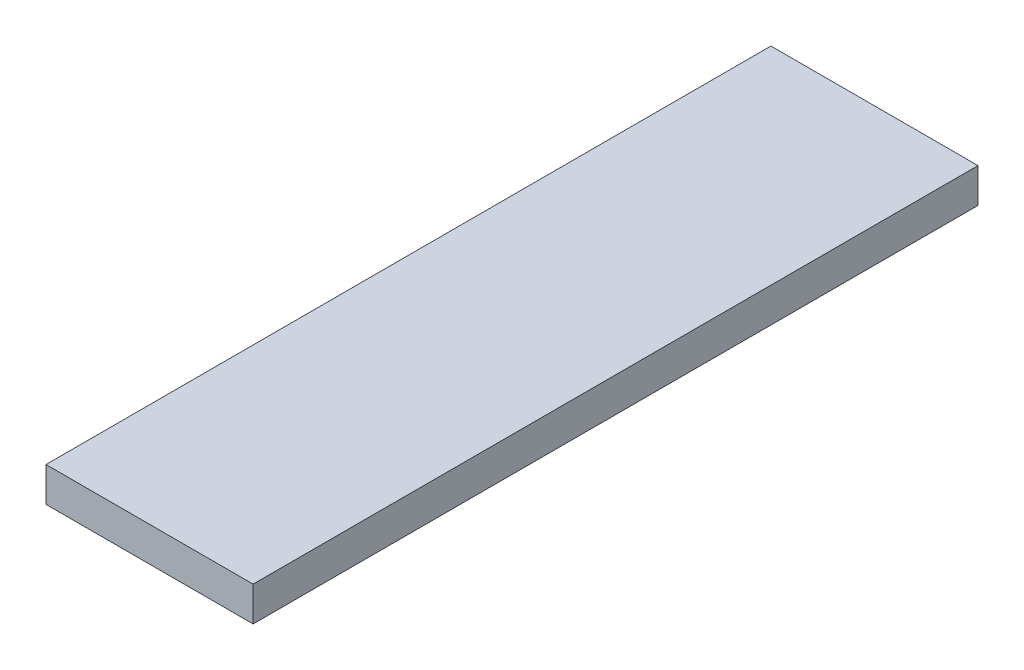
SolidWorks part; units mm, degrees
ref_plane "Front" through (0, 0, 0) normal (0, 0, 1) x (1, 0, 0)
ref_plane "Top" through (0, 0, 0) normal (0, 1, 0) x (1, 0, 0)
ref_plane "Right" through (0, 0, 0) normal (1, 0, 0) x (0, 0, -1)
sketch "Sketch1" plane through (0, 0, 0) normal (0, 0, 1) x (1, 0, 0)
  line L1 (0, 0) -> (-15.24, 0)
  line L2 (0, 0) -> (0, 2.54)
  line L3 (0, 2.54) -> (-15.24, 2.54)
  line L4 (-15.24, 0) -> (-15.24, 2.54)
  dimension "D1" = 15.24
  dimension "D2" = 2.54
extrude "Boss-Extrude1" add sketch "Sketch1" along normal blind 53.34
